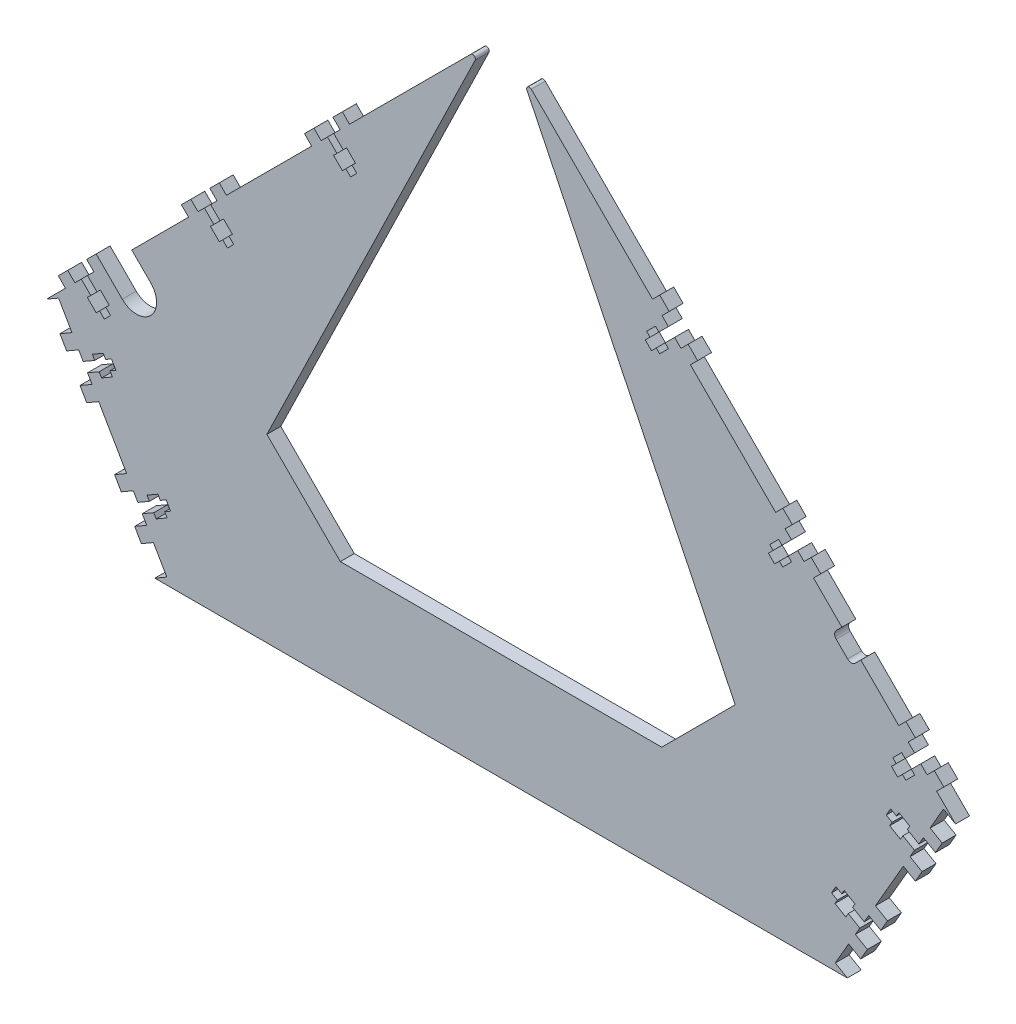
SolidWorks part; units mm, degrees
material "Acrylic (Blue)"
ref_plane "Front Plane" through (0, 0, 0) normal (0, 0, 1) x (1, 0, 0)
ref_plane "Top Plane" through (0, 0, 0) normal (0, 1, 0) x (1, 0, 0)
ref_plane "Right Plane" through (0, 0, 0) normal (1, 0, 0) x (0, 0, -1)
sketch "Sketch1" plane through (0, 0, 0) normal (0, 0, 1) x (1, 0, 0)
  line L0 (0, 0) -> (0, 304.4261) construction
  line L1 (0, 304.4261) -> (215.5261, 88.9)
  line L2 (215.5261, 88.9) -> (164.1997, 0)
  line L3 (164.1997, 0) -> (0, 0)
  line L4 (0, 304.4261) -> (-215.5261, 88.9)
  line L5 (-215.5261, 88.9) -> (-164.1997, 0)
  line L6 (-164.1997, 0) -> (0, 0)
  line L7 (-215.5261, 88.9) -> (215.5261, 88.9) construction
  line L8 (0, 304.4261) -> (3.5921, 308.0182) construction
  line L9 (3.5921, 308.0182) -> (219.1182, 92.4921) construction
  line L10 (219.1182, 92.4921) -> (215.5261, 88.9) construction
  line L11 (3.5921, 308.0182) -> (0, 311.6104) construction
  line L12 (0, 311.6104) -> (-219.1182, 92.4921) construction
  line L13 (-219.1182, 92.4921) -> (-215.5261, 88.9) construction
  line L14 (215.5261, 88.9) -> (219.9256, 86.36) construction
  line L15 (219.9256, 86.36) -> (168.5991, -2.54) construction
  line L16 (168.5991, -2.54) -> (164.1997, 0) construction
  line L17 (164.1997, 0) -> (164.1997, -12.7) construction
  line L18 (164.1997, -12.7) -> (-164.1997, -12.7) construction
  line L19 (-164.1997, -12.7) -> (-164.1997, 0) construction
  line L20 (-164.1997, 0) -> (-168.5991, -2.54) construction
  line L21 (-168.5991, -2.54) -> (-219.9256, 86.36) construction
  line L22 (-219.9256, 86.36) -> (-215.5261, 88.9) construction
  dimension "D1" = 304.8
  dimension "D2" = 120
  dimension "D3" = 88.9
  dimension "D4" = 5.08
  dimension "D5" = 12.7
extrude "Boss-Extrude1" add sketch "Sketch1" along normal blind 6.604
other "Move Face2" face at (107.7631, 196.6631, 3.302) parameters "D1"=0.0025
sketch "Sketch2" plane through (0, 0, 6.604) normal (0, 0, 1) x (1, 0, 0)
  line L0 (215.5275, 88.9023) -> (0.0018, 304.4279) construction
  line L1 (0, 0) -> (0, 311.15) construction
  line L2 (0, 50.8) -> (76.2, 50.8)
  line L3 (0.0018, 304.4279) -> (3.5939, 308.02) construction
  line L4 (76.2, 50.8) -> (111.0333, 85.6333)
  line L5 (8.9816, 295.4482) -> (-8.9803, 295.4459) construction
  line L6 (0.0018, 304.4279) -> (-215.5261, 88.9) construction
  line L7 (-8.9803, 295.4459) -> (-111.0333, 85.6333)
  line L8 (-164.1997, 0) -> (164.1997, 0) construction
  line L9 (111.0333, 85.6333) -> (8.9816, 295.4482)
  line L10 (3.5939, 308.02) -> (0.0018, 311.6121) construction
  line L11 (-8.9803, 295.4459) -> (0.0018, 304.4279)
  line L12 (-111.0333, 85.6333) -> (-76.2, 50.8)
  line L13 (-76.2, 50.8) -> (0, 50.8)
  line L14 (0.0018, 304.4279) -> (8.9816, 295.4482)
  line L15 (0.0018, 304.4279) -> (-215.5261, 88.9) construction
  dimension "D1" = 260.35
  dimension "D2" = 50.8
  dimension "D3" = 292.1
  dimension "D4" = 5.08
  dimension "D6" = 76.2
  dimension "D7" = 45
  dimension "D8" = 76.2
  dimension "D9" = 45
  dimension "D10" = 292.1
extrude "Cut-Extrude1" cut sketch "Sketch2" against normal through all
sketch "Sketch3" plane through (0, 0, 6.604) normal (0, 0, 1) x (1, 0, 0)
  line L0 (-209.8069, 92.202) -> (-215.5261, 88.9)
  line L1 (-215.5261, 88.9) -> (-164.1997, 0)
  line L2 (-164.1997, 0) -> (-158.4805, 3.302)
  line L3 (-158.4805, 3.302) -> (-209.8069, 92.202)
  line L4 (0, 304.4261) -> (0, 0) construction
  line L5 (158.4805, 3.302) -> (209.8069, 92.202)
  line L6 (164.1997, 0) -> (158.4805, 3.302)
  line L7 (215.5261, 88.9) -> (164.1997, 0)
  line L8 (209.8069, 92.202) -> (215.5261, 88.9)
  dimension "D1" = 6.604
extrude "Cut-Extrude2" cut sketch "Sketch3" against normal through all
sketch "Sketch4" plane through (0, 0, 6.604) normal (0, 0, 1) x (1, 0, 0)
  line L0 (-8.9803, 295.4459) -> (-215.5261, 88.9) construction
  line L1 (-93.2151, 218.0361) -> (-133.6262, 177.6249) construction
  line L2 (-8.9803, 295.4459) -> (-215.5261, 88.9) construction
  line L3 (-191.9979, 119.2533) -> (-151.5867, 159.6644) construction
  line L6 (215.5275, 88.9023) -> (8.9816, 295.4482) construction
  line L7 (93.2164, 218.0384) -> (133.6275, 177.6272) construction
  line L8 (-158.4805, 3.302) -> (-209.8069, 92.202) construction
  line L9 (-209.8069, 92.202) -> (-215.5261, 88.9) construction
  line L10 (151.588, 159.6667) -> (191.9992, 119.2555) construction
  line L11 (209.8069, 92.202) -> (158.4805, 3.302) construction
  line L12 (158.4805, 3.302) -> (164.1997, 0) construction
  line L13 (-164.1997, 0) -> (-158.4805, 3.302) construction
  line L14 (215.5261, 88.9) -> (209.8069, 92.202) construction
  line B0 (-82.2951, 222.1311) -> (-77.8049, 217.641) construction
  line B1 (-77.8049, 217.641) -> (-79.4214, 216.0245) construction
  line B2 (-79.4214, 216.0245) -> (-75.2186, 211.8217) construction
  line B3 (-75.2186, 211.8217) -> (-73.6022, 213.4382) construction
  line B4 (-73.6022, 213.4382) -> (-71.3392, 211.1752) construction
  line B5 (-71.3392, 211.1752) -> (-68.3936, 214.1207) construction
  line B6 (-68.3936, 214.1207) -> (-70.6567, 216.3837) construction
  line B7 (-70.6567, 216.3837) -> (-69.0402, 218.0002) construction
  line B8 (-69.0402, 218.0002) -> (-73.243, 222.2029) construction
  line B9 (-73.243, 222.2029) -> (-74.8594, 220.5865) construction
  line B10 (-74.8594, 220.5865) -> (-79.3495, 225.0766) construction
  line B11 (-76.3322, 228.094) -> (-79.7447, 231.5065) construction
  line B12 (-79.7447, 231.5065) -> (-75.2545, 235.9966) construction
  line B13 (-75.2545, 235.9966) -> (-71.842, 232.5841) construction
  line B14 (-82.2951, 222.1311) -> (-85.3124, 219.1137) construction
  line B15 (-85.3124, 219.1137) -> (-88.7249, 222.5262) construction
  line B16 (-88.7249, 222.5262) -> (-93.2151, 218.0361) construction
  line B17 (-93.2151, 218.0361) -> (-89.8026, 214.6236) construction
  line B18 (-79.3495, 225.0766) -> (-82.2951, 222.1311) construction
  line B19 (-199.0384, 105.3878) -> (-194.5483, 100.8976) construction
  line B20 (-194.5483, 100.8976) -> (-196.1647, 99.2812) construction
  line B21 (-196.1647, 99.2812) -> (-191.962, 95.0784) construction
  line B22 (-191.962, 95.0784) -> (-190.3455, 96.6949) construction
  line B23 (-190.3455, 96.6949) -> (-188.0825, 94.4318) construction
  line B24 (-188.0825, 94.4318) -> (-185.137, 97.3774) construction
  line B25 (-185.137, 97.3774) -> (-187.4, 99.6404) construction
  line B26 (-187.4, 99.6404) -> (-185.7835, 101.2568) construction
  line B27 (-185.7835, 101.2568) -> (-189.9863, 105.4596) construction
  line B28 (-189.9863, 105.4596) -> (-191.6027, 103.8431) construction
  line B29 (-191.6027, 103.8431) -> (-196.0929, 108.3333) construction
  line B30 (-196.0929, 108.3333) -> (-193.0755, 111.3506) construction
  line B31 (-193.0755, 111.3506) -> (-196.488, 114.7631) construction
  line B32 (-196.488, 114.7631) -> (-191.9979, 119.2533) construction
  line B33 (-191.9979, 119.2533) -> (-188.5854, 115.8408) construction
  line B34 (-199.0384, 105.3878) -> (-202.0558, 102.3704) construction
  line B35 (-202.0558, 102.3704) -> (-205.4683, 105.7829) construction
  line B36 (-205.4683, 105.7829) -> (-209.9584, 101.2928) construction
  line B37 (-209.9584, 101.2928) -> (-206.5459, 97.8803) construction
  line B38 (-196.0929, 108.3333) -> (-199.0384, 105.3878) construction
  line B39 (-170.1391, 23.4953) -> (-164.6398, 26.6703) construction
  line B40 (-164.6398, 26.6703) -> (-163.4968, 24.6906) construction
  line B41 (-163.4968, 24.6906) -> (-158.3495, 27.6624) construction
  line B42 (-158.3495, 27.6624) -> (-159.4925, 29.6421) construction
  line B43 (-159.4925, 29.6421) -> (-156.7209, 31.2423) construction
  line B44 (-156.7209, 31.2423) -> (-158.8037, 34.8498) construction
  line B45 (-158.8037, 34.8498) -> (-161.5753, 33.2496) construction
  line B46 (-161.5753, 33.2496) -> (-162.7183, 35.2293) construction
  line B47 (-162.7183, 35.2293) -> (-167.8656, 32.2575) construction
  line B48 (-167.8656, 32.2575) -> (-166.7226, 30.2778) construction
  line B49 (-166.7226, 30.2778) -> (-172.2219, 27.1028) construction
  line B50 (-172.2219, 27.1028) -> (-174.3555, 30.7983) construction
  line B51 (-174.3555, 30.7983) -> (-178.5349, 28.3853) construction
  line B52 (-178.5349, 28.3853) -> (-181.7099, 33.8846) construction
  line B53 (-181.7099, 33.8846) -> (-177.5305, 36.2976) construction
  line B54 (-168.0055, 19.7998) -> (-172.1849, 17.3868) construction
  line B55 (-172.1849, 17.3868) -> (-169.0099, 11.8875) construction
  line B56 (-169.0099, 11.8875) -> (-164.8305, 14.3005) construction
  line B57 (-172.2219, 27.1028) -> (-170.1391, 23.4953) construction
  line B58 (-196.0655, 68.4012) -> (-190.5663, 71.5762) construction
  line B59 (-190.5663, 71.5762) -> (-189.4233, 69.5965) construction
  line B60 (-189.4233, 69.5965) -> (-184.2759, 72.5683) construction
  line B61 (-184.2759, 72.5683) -> (-185.4189, 74.548) construction
  line B62 (-185.4189, 74.548) -> (-182.6473, 76.1482) construction
  line B63 (-182.6473, 76.1482) -> (-184.7301, 79.7557) construction
  line B64 (-184.7301, 79.7557) -> (-187.5017, 78.1555) construction
  line B65 (-187.5017, 78.1555) -> (-188.6447, 80.1352) construction
  line B66 (-188.6447, 80.1352) -> (-193.7921, 77.1634) construction
  line B67 (-193.7921, 77.1634) -> (-192.6491, 75.1837) construction
  line B68 (-192.6491, 75.1837) -> (-198.1483, 72.0087) construction
  line B69 (-198.1483, 72.0087) -> (-200.2819, 75.7042) construction
  line B70 (-200.2819, 75.7042) -> (-204.4614, 73.2912) construction
  line B71 (-204.4614, 73.2912) -> (-207.6364, 78.7905) construction
  line B72 (-207.6364, 78.7905) -> (-203.4569, 81.2035) construction
  line B73 (-196.0655, 68.4012) -> (-193.9319, 64.7057) construction
  line B74 (-193.9319, 64.7057) -> (-198.1114, 62.2927) construction
  line B75 (-198.1114, 62.2927) -> (-194.9364, 56.7934) construction
  line B76 (-194.9364, 56.7934) -> (-190.7569, 59.2064) construction
  line B77 (-198.1483, 72.0087) -> (-196.0655, 68.4012) construction
  line B78 (172.2219, 27.1028) -> (166.7226, 30.2778) construction
  line B79 (166.7226, 30.2778) -> (167.8656, 32.2575) construction
  line B80 (167.8656, 32.2575) -> (162.7183, 35.2293) construction
  line B81 (162.7183, 35.2293) -> (161.5753, 33.2496) construction
  line B82 (161.5753, 33.2496) -> (158.8037, 34.8498) construction
  line B83 (158.8037, 34.8498) -> (156.7209, 31.2423) construction
  line B84 (156.7209, 31.2423) -> (159.4925, 29.6421) construction
  line B85 (159.4925, 29.6421) -> (158.3495, 27.6624) construction
  line B86 (158.3495, 27.6624) -> (163.4968, 24.6906) construction
  line B87 (163.4968, 24.6906) -> (164.6398, 26.6703) construction
  line B88 (164.6398, 26.6703) -> (170.1391, 23.4953) construction
  line B89 (168.0055, 19.7998) -> (172.1849, 17.3868) construction
  line B90 (172.1849, 17.3868) -> (169.0099, 11.8875) construction
  line B91 (169.0099, 11.8875) -> (164.8305, 14.3005) construction
  line B92 (172.2219, 27.1028) -> (174.3555, 30.7983) construction
  line B93 (174.3555, 30.7983) -> (178.5349, 28.3853) construction
  line B94 (178.5349, 28.3853) -> (181.7099, 33.8846) construction
  line B95 (181.7099, 33.8846) -> (177.5305, 36.2976) construction
  line B96 (170.1391, 23.4953) -> (172.2219, 27.1028) construction
  line B97 (198.1483, 72.0087) -> (192.6491, 75.1837) construction
  line B98 (192.6491, 75.1837) -> (193.7921, 77.1634) construction
  line B99 (193.7921, 77.1634) -> (188.6447, 80.1352) construction
  line B100 (188.6447, 80.1352) -> (187.5017, 78.1555) construction
  line B101 (187.5017, 78.1555) -> (184.7301, 79.7557) construction
  line B102 (184.7301, 79.7557) -> (182.6473, 76.1482) construction
  line B103 (182.6473, 76.1482) -> (185.4189, 74.548) construction
  line B104 (185.4189, 74.548) -> (184.2759, 72.5683) construction
  line B105 (184.2759, 72.5683) -> (189.4233, 69.5965) construction
  line B106 (189.4233, 69.5965) -> (190.5663, 71.5762) construction
  line B107 (190.5663, 71.5762) -> (196.0655, 68.4012) construction
  line B108 (196.0655, 68.4012) -> (193.9319, 64.7057) construction
  line B109 (193.9319, 64.7057) -> (198.1114, 62.2927) construction
  line B110 (198.1114, 62.2927) -> (194.9364, 56.7934) construction
  line B111 (194.9364, 56.7934) -> (190.7569, 59.2064) construction
  line B112 (200.2819, 75.7042) -> (204.4614, 73.2912) construction
  line B113 (204.4614, 73.2912) -> (207.6364, 78.7905) construction
  line B114 (207.6364, 78.7905) -> (203.4569, 81.2035) construction
  line B115 (196.0655, 68.4012) -> (198.1483, 72.0087) construction
  line B116 (196.0942, 108.3356) -> (191.6041, 103.8454) construction
  line B117 (191.6041, 103.8454) -> (189.9876, 105.4619) construction
  line B118 (189.9876, 105.4619) -> (185.7849, 101.2591) construction
  line B119 (185.7849, 101.2591) -> (187.4013, 99.6427) construction
  line B120 (187.4013, 99.6427) -> (185.1383, 97.3796) construction
  line B121 (185.1383, 97.3796) -> (188.0838, 94.4341) construction
  line B122 (188.0838, 94.4341) -> (190.3468, 96.6971) construction
  line B123 (190.3468, 96.6971) -> (191.9633, 95.0807) construction
  line B124 (191.9633, 95.0807) -> (196.166, 99.2835) construction
  line B125 (196.166, 99.2835) -> (194.5496, 100.8999) construction
  line B126 (194.5496, 100.8999) -> (199.0397, 105.39) construction
  line B127 (199.0397, 105.39) -> (202.0571, 102.3727) construction
  line B128 (202.0571, 102.3727) -> (205.4696, 105.7852) construction
  line B129 (205.4696, 105.7852) -> (209.9597, 101.295) construction
  line B130 (209.9597, 101.295) -> (206.5472, 97.8825) construction
  line B131 (196.0942, 108.3356) -> (193.0768, 111.3529) construction
  line B132 (193.0768, 111.3529) -> (196.4893, 114.7654) construction
  line B133 (196.4893, 114.7654) -> (191.9992, 119.2555) construction
  line B134 (191.9992, 119.2555) -> (188.5867, 115.843) construction
  line B135 (199.0397, 105.39) -> (196.0942, 108.3356) construction
  line B136 (137.7225, 166.7072) -> (133.2324, 162.2171) construction
  line B137 (133.2324, 162.2171) -> (131.6159, 163.8335) construction
  line B138 (131.6159, 163.8335) -> (127.4132, 159.6308) construction
  line B139 (127.4132, 159.6308) -> (129.0296, 158.0143) construction
  line B140 (129.0296, 158.0143) -> (126.7666, 155.7513) construction
  line B141 (126.7666, 155.7513) -> (129.7121, 152.8058) construction
  line B142 (129.7121, 152.8058) -> (131.9752, 155.0688) construction
  line B143 (131.9752, 155.0688) -> (133.5916, 153.4524) construction
  line B144 (133.5916, 153.4524) -> (137.7944, 157.6551) construction
  line B145 (137.7944, 157.6551) -> (136.1779, 159.2716) construction
  line B146 (136.1779, 159.2716) -> (140.668, 163.7617) construction
  line B147 (140.668, 163.7617) -> (143.6854, 160.7443) construction
  line B148 (143.6854, 160.7443) -> (147.0979, 164.1568) construction
  line B149 (147.0979, 164.1568) -> (151.588, 159.6667) construction
  line B150 (151.588, 159.6667) -> (148.1755, 156.2542) construction
  line B151 (137.7225, 166.7072) -> (134.7052, 169.7246) construction
  line B152 (134.7052, 169.7246) -> (138.1177, 173.1371) construction
  line B153 (138.1177, 173.1371) -> (133.6275, 177.6272) construction
  line B154 (133.6275, 177.6272) -> (130.215, 174.2147) construction
  line B155 (140.668, 163.7617) -> (137.7225, 166.7072) construction
  line B156 (79.3509, 225.0789) -> (74.8607, 220.5888) construction
  line B157 (74.8607, 220.5888) -> (73.2443, 222.2052) construction
  line B158 (73.2443, 222.2052) -> (69.0415, 218.0024) construction
  line B159 (69.0415, 218.0024) -> (70.658, 216.386) construction
  line B160 (70.658, 216.386) -> (68.3949, 214.123) construction
  line B161 (68.3949, 214.123) -> (71.3405, 211.1774) construction
  line B162 (71.3405, 211.1774) -> (73.6035, 213.4405) construction
  line B163 (73.6035, 213.4405) -> (75.2199, 211.824) construction
  line B164 (75.2199, 211.824) -> (79.4227, 216.0268) construction
  line B165 (79.4227, 216.0268) -> (77.8063, 217.6432) construction
  line B166 (77.8063, 217.6432) -> (82.2964, 222.1334) construction
  line B167 (82.2964, 222.1334) -> (85.3137, 219.116) construction
  line B168 (85.3137, 219.116) -> (88.7262, 222.5285) construction
  line B169 (88.7262, 222.5285) -> (93.2164, 218.0384) construction
  line B170 (93.2164, 218.0384) -> (89.8039, 214.6259) construction
  line B171 (79.3509, 225.0789) -> (76.3335, 228.0962) construction
  line B172 (76.3335, 228.0962) -> (79.746, 231.5087) construction
  line B173 (79.746, 231.5087) -> (75.2559, 235.9989) construction
  line B174 (75.2559, 235.9989) -> (71.8434, 232.5864) construction
  line B175 (82.2964, 222.1334) -> (79.3509, 225.0789) construction
  line B176 (-140.6667, 163.7594) -> (-136.1766, 159.2693) construction
  line B177 (-136.1766, 159.2693) -> (-137.793, 157.6528) construction
  line B178 (-137.793, 157.6528) -> (-133.5903, 153.4501) construction
  line B179 (-133.5903, 153.4501) -> (-131.9738, 155.0665) construction
  line B180 (-131.9738, 155.0665) -> (-129.7108, 152.8035) construction
  line B181 (-129.7108, 152.8035) -> (-126.7653, 155.749) construction
  line B182 (-126.7653, 155.749) -> (-129.0283, 158.0121) construction
  line B183 (-129.0283, 158.0121) -> (-127.4119, 159.6285) construction
  line B184 (-127.4119, 159.6285) -> (-131.6146, 163.8313) construction
  line B185 (-131.6146, 163.8313) -> (-133.2311, 162.2148) construction
  line B186 (-133.2311, 162.2148) -> (-137.7212, 166.7049) construction
  line B187 (-137.7212, 166.7049) -> (-134.7038, 169.7223) construction
  line B188 (-134.7038, 169.7223) -> (-138.1163, 173.1348) construction
  line B189 (-138.1163, 173.1348) -> (-133.6262, 177.6249) construction
  line B190 (-133.6262, 177.6249) -> (-130.2137, 174.2124) construction
  line B191 (-140.6667, 163.7594) -> (-143.6841, 160.742) construction
  line B192 (-143.6841, 160.742) -> (-147.0966, 164.1545) construction
  line B193 (-147.0966, 164.1545) -> (-151.5867, 159.6644) construction
  line B194 (-151.5867, 159.6644) -> (-148.1742, 156.2519) construction
  line B195 (-137.7212, 166.7049) -> (-140.6667, 163.7594) construction
  dimension "D1" = 12.7
  dimension "D2" = 190.5
  dimension "D3" = 12.7
  dimension "D4" = 190.5
  dimension "D5" = 12.7
  dimension "D6" = 12.7
  dimension "D7" = 12.7
  dimension "D8" = 12.7
sketch_block_instance "NUT_HOLE-1"
sketch_block "NUT_HOLE" parameters "D1"=6.35, "D2"=4.1656, "D3"=25.4, "D4"=4.826, "D5"=8.7376, "D6"=5.9436, "D7"=6.35, "D8"=20.32
sketch_block_instance "NUT_HOLE-3"
sketch_block_instance "NUT_HOLE-9"
sketch_block_instance "NUT_HOLE-10"
sketch_block_instance "NUT_HOLE-11"
sketch_block_instance "NUT_HOLE-12"
sketch_block_instance "NUT_HOLE-13"
sketch_block_instance "NUT_HOLE-14"
sketch_block_instance "NUT_HOLE-15"
sketch_block_instance "NUT_HOLE-16"
sketch "Sketch6" plane through (0, 0, 6.604) normal (0, 0, 1) x (1, 0, 0)
  line L0 (-133.2311, 162.2148) -> (-137.7212, 166.7049) construction
  line L1 (-140.6667, 163.7594) -> (-136.1766, 159.2693) construction
  line L2 (-136.1766, 159.2693) -> (-137.793, 157.6528) construction
  line L3 (-137.793, 157.6528) -> (-133.5903, 153.4501) construction
  line L4 (-133.5903, 153.4501) -> (-131.9738, 155.0665) construction
  line L5 (-131.9738, 155.0665) -> (-129.7108, 152.8035) construction
  line L6 (-129.7108, 152.8035) -> (-126.7653, 155.749) construction
  line L7 (-126.7653, 155.749) -> (-129.0283, 158.0121) construction
  line L8 (-129.0283, 158.0121) -> (-127.4119, 159.6285) construction
  line L9 (-127.4119, 159.6285) -> (-131.6146, 163.8313) construction
  line L10 (-131.6146, 163.8313) -> (-133.2311, 162.2148) construction
  line L11 (-133.2311, 162.2148) -> (-137.7212, 166.7049)
  line L12 (-140.6667, 163.7594) -> (-136.1766, 159.2693)
  line L13 (-136.1766, 159.2693) -> (-137.793, 157.6528)
  line L14 (-137.793, 157.6528) -> (-133.5903, 153.4501)
  line L15 (-133.5903, 153.4501) -> (-131.9738, 155.0665)
  line L16 (-131.9738, 155.0665) -> (-129.7108, 152.8035)
  line L17 (-129.7108, 152.8035) -> (-126.7653, 155.749)
  line L18 (-126.7653, 155.749) -> (-129.0283, 158.0121)
  line L19 (-129.0283, 158.0121) -> (-127.4119, 159.6285)
  line L20 (-127.4119, 159.6285) -> (-131.6146, 163.8313)
  line L21 (-131.6146, 163.8313) -> (-133.2311, 162.2148)
  line L22 (-140.6667, 163.7594) -> (-137.7212, 166.7049)
  line L110 (-74.8594, 220.5865) -> (-79.3495, 225.0766) construction
  line L111 (-73.243, 222.2029) -> (-74.8594, 220.5865) construction
  line L112 (-69.0402, 218.0002) -> (-73.243, 222.2029) construction
  line L113 (-70.6567, 216.3837) -> (-69.0402, 218.0002) construction
  line L114 (-68.3936, 214.1207) -> (-70.6567, 216.3837) construction
  line L115 (-71.3392, 211.1752) -> (-68.3936, 214.1207) construction
  line L116 (-73.6022, 213.4382) -> (-71.3392, 211.1752) construction
  line L117 (-75.2186, 211.8217) -> (-73.6022, 213.4382) construction
  line L118 (-79.4214, 216.0245) -> (-75.2186, 211.8217) construction
  line L119 (-77.8049, 217.641) -> (-79.4214, 216.0245) construction
  line L120 (-82.2951, 222.1311) -> (-77.8049, 217.641) construction
  line L121 (-74.8594, 220.5865) -> (-79.3495, 225.0766)
  line L122 (-73.243, 222.2029) -> (-74.8594, 220.5865)
  line L123 (-69.0402, 218.0002) -> (-73.243, 222.2029)
  line L124 (-70.6567, 216.3837) -> (-69.0402, 218.0002)
  line L125 (-68.3936, 214.1207) -> (-70.6567, 216.3837)
  line L126 (-71.3392, 211.1752) -> (-68.3936, 214.1207)
  line L127 (-73.6022, 213.4382) -> (-71.3392, 211.1752)
  line L128 (-75.2186, 211.8217) -> (-73.6022, 213.4382)
  line L129 (-79.4214, 216.0245) -> (-75.2186, 211.8217)
  line L130 (-77.8049, 217.641) -> (-79.4214, 216.0245)
  line L131 (-82.2951, 222.1311) -> (-77.8049, 217.641)
  line L154 (-191.6027, 103.8431) -> (-196.0929, 108.3333) construction
  line L155 (-199.0384, 105.3878) -> (-194.5483, 100.8976) construction
  line L156 (-194.5483, 100.8976) -> (-196.1647, 99.2812) construction
  line L157 (-196.1647, 99.2812) -> (-191.962, 95.0784) construction
  line L158 (-189.9863, 105.4596) -> (-191.6027, 103.8431) construction
  line L159 (-185.7835, 101.2568) -> (-189.9863, 105.4596) construction
  line L160 (-187.4, 99.6404) -> (-185.7835, 101.2568) construction
  line L161 (-185.137, 97.3774) -> (-187.4, 99.6404) construction
  line L162 (-188.0825, 94.4318) -> (-185.137, 97.3774) construction
  line L163 (-190.3455, 96.6949) -> (-188.0825, 94.4318) construction
  line L164 (-191.962, 95.0784) -> (-190.3455, 96.6949) construction
  line L165 (-192.6491, 75.1837) -> (-198.1483, 72.0087) construction
  line L166 (-193.7921, 77.1634) -> (-192.6491, 75.1837) construction
  line L167 (-188.6447, 80.1352) -> (-193.7921, 77.1634) construction
  line L168 (-184.7301, 79.7557) -> (-187.5017, 78.1555) construction
  line L169 (-182.6473, 76.1482) -> (-184.7301, 79.7557) construction
  line L170 (-187.5017, 78.1555) -> (-188.6447, 80.1352) construction
  line L171 (-185.4189, 74.548) -> (-182.6473, 76.1482) construction
  line L172 (-184.2759, 72.5683) -> (-185.4189, 74.548) construction
  line L173 (-189.4233, 69.5965) -> (-184.2759, 72.5683) construction
  line L174 (-190.5663, 71.5762) -> (-189.4233, 69.5965) construction
  line L175 (-196.0655, 68.4012) -> (-190.5663, 71.5762) construction
  line L176 (-191.6027, 103.8431) -> (-196.0929, 108.3333)
  line L177 (-199.0384, 105.3878) -> (-194.5483, 100.8976)
  line L178 (-194.5483, 100.8976) -> (-196.1647, 99.2812)
  line L179 (-196.1647, 99.2812) -> (-191.962, 95.0784)
  line L180 (-189.9863, 105.4596) -> (-191.6027, 103.8431)
  line L181 (-185.7835, 101.2568) -> (-189.9863, 105.4596)
  line L182 (-187.4, 99.6404) -> (-185.7835, 101.2568)
  line L183 (-185.137, 97.3774) -> (-187.4, 99.6404)
  line L184 (-188.0825, 94.4318) -> (-185.137, 97.3774)
  line L185 (-190.3455, 96.6949) -> (-188.0825, 94.4318)
  line L186 (-191.962, 95.0784) -> (-190.3455, 96.6949)
  line L187 (-192.6491, 75.1837) -> (-198.1483, 72.0087)
  line L188 (-193.7921, 77.1634) -> (-192.6491, 75.1837)
  line L189 (-188.6447, 80.1352) -> (-193.7921, 77.1634)
  line L190 (-184.7301, 79.7557) -> (-187.5017, 78.1555)
  line L191 (-182.6473, 76.1482) -> (-184.7301, 79.7557)
  line L192 (-187.5017, 78.1555) -> (-188.6447, 80.1352)
  line L193 (-185.4189, 74.548) -> (-182.6473, 76.1482)
  line L194 (-184.2759, 72.5683) -> (-185.4189, 74.548)
  line L195 (-189.4233, 69.5965) -> (-184.2759, 72.5683)
  line L196 (-190.5663, 71.5762) -> (-189.4233, 69.5965)
  line L197 (-196.0655, 68.4012) -> (-190.5663, 71.5762)
  line L198 (-166.7226, 30.2778) -> (-172.2219, 27.1028) construction
  line L199 (-167.8656, 32.2575) -> (-166.7226, 30.2778) construction
  line L200 (-162.7183, 35.2293) -> (-167.8656, 32.2575) construction
  line L201 (-161.5753, 33.2496) -> (-162.7183, 35.2293) construction
  line L202 (-158.8037, 34.8498) -> (-161.5753, 33.2496) construction
  line L203 (-156.7209, 31.2423) -> (-158.8037, 34.8498) construction
  line L204 (-159.4925, 29.6421) -> (-156.7209, 31.2423) construction
  line L205 (-158.3495, 27.6624) -> (-159.4925, 29.6421) construction
  line L206 (-163.4968, 24.6906) -> (-158.3495, 27.6624) construction
  line L207 (-164.6398, 26.6703) -> (-163.4968, 24.6906) construction
  line L208 (-170.1391, 23.4953) -> (-164.6398, 26.6703) construction
  line L209 (-166.7226, 30.2778) -> (-172.2219, 27.1028)
  line L210 (-167.8656, 32.2575) -> (-166.7226, 30.2778)
  line L211 (-162.7183, 35.2293) -> (-167.8656, 32.2575)
  line L212 (-161.5753, 33.2496) -> (-162.7183, 35.2293)
  line L213 (-158.8037, 34.8498) -> (-161.5753, 33.2496)
  line L214 (-156.7209, 31.2423) -> (-158.8037, 34.8498)
  line L215 (-159.4925, 29.6421) -> (-156.7209, 31.2423)
  line L216 (-158.3495, 27.6624) -> (-159.4925, 29.6421)
  line L217 (-163.4968, 24.6906) -> (-158.3495, 27.6624)
  line L218 (-164.6398, 26.6703) -> (-163.4968, 24.6906)
  line L219 (-170.1391, 23.4953) -> (-164.6398, 26.6703)
  line L220 (158.3495, 27.6624) -> (163.4968, 24.6906) construction
  line L221 (159.4925, 29.6421) -> (158.3495, 27.6624) construction
  line L222 (156.7209, 31.2423) -> (159.4925, 29.6421) construction
  line L223 (158.8037, 34.8498) -> (156.7209, 31.2423) construction
  line L224 (161.5753, 33.2496) -> (158.8037, 34.8498) construction
  line L225 (167.8656, 32.2575) -> (162.7183, 35.2293) construction
  line L226 (162.7183, 35.2293) -> (161.5753, 33.2496) construction
  line L227 (172.2219, 27.1028) -> (166.7226, 30.2778) construction
  line L228 (164.6398, 26.6703) -> (170.1391, 23.4953) construction
  line L229 (163.4968, 24.6906) -> (164.6398, 26.6703) construction
  line L230 (166.7226, 30.2778) -> (167.8656, 32.2575) construction
  line L231 (198.1483, 72.0087) -> (192.6491, 75.1837) construction
  line L232 (192.6491, 75.1837) -> (193.7921, 77.1634) construction
  line L233 (193.7921, 77.1634) -> (188.6447, 80.1352) construction
  line L234 (188.6447, 80.1352) -> (187.5017, 78.1555) construction
  line L235 (187.5017, 78.1555) -> (184.7301, 79.7557) construction
  line L236 (184.7301, 79.7557) -> (182.6473, 76.1482) construction
  line L237 (182.6473, 76.1482) -> (185.4189, 74.548) construction
  line L238 (185.4189, 74.548) -> (184.2759, 72.5683) construction
  line L239 (184.2759, 72.5683) -> (189.4233, 69.5965) construction
  line L240 (189.4233, 69.5965) -> (190.5663, 71.5762) construction
  line L241 (190.5663, 71.5762) -> (196.0655, 68.4012) construction
  line L242 (158.3495, 27.6624) -> (163.4968, 24.6906)
  line L243 (159.4925, 29.6421) -> (158.3495, 27.6624)
  line L244 (156.7209, 31.2423) -> (159.4925, 29.6421)
  line L245 (158.8037, 34.8498) -> (156.7209, 31.2423)
  line L246 (161.5753, 33.2496) -> (158.8037, 34.8498)
  line L247 (167.8656, 32.2575) -> (162.7183, 35.2293)
  line L248 (162.7183, 35.2293) -> (161.5753, 33.2496)
  line L249 (172.2219, 27.1028) -> (166.7226, 30.2778)
  line L250 (164.6398, 26.6703) -> (170.1391, 23.4953)
  line L251 (163.4968, 24.6906) -> (164.6398, 26.6703)
  line L252 (166.7226, 30.2778) -> (167.8656, 32.2575)
  line L253 (198.1483, 72.0087) -> (192.6491, 75.1837)
  line L254 (192.6491, 75.1837) -> (193.7921, 77.1634)
  line L255 (193.7921, 77.1634) -> (188.6447, 80.1352)
  line L256 (188.6447, 80.1352) -> (187.5017, 78.1555)
  line L257 (187.5017, 78.1555) -> (184.7301, 79.7557)
  line L258 (184.7301, 79.7557) -> (182.6473, 76.1482)
  line L259 (182.6473, 76.1482) -> (185.4189, 74.548)
  line L260 (185.4189, 74.548) -> (184.2759, 72.5683)
  line L261 (184.2759, 72.5683) -> (189.4233, 69.5965)
  line L262 (189.4233, 69.5965) -> (190.5663, 71.5762)
  line L263 (190.5663, 71.5762) -> (196.0655, 68.4012)
  line L264 (187.4013, 99.6427) -> (185.1383, 97.3796) construction
  line L265 (185.1383, 97.3796) -> (188.0838, 94.4341) construction
  line L266 (188.0838, 94.4341) -> (190.3468, 96.6971) construction
  line L267 (190.3468, 96.6971) -> (191.9633, 95.0807) construction
  line L268 (191.9633, 95.0807) -> (196.166, 99.2835) construction
  line L269 (196.166, 99.2835) -> (194.5496, 100.8999) construction
  line L270 (194.5496, 100.8999) -> (199.0397, 105.39) construction
  line L271 (196.0942, 108.3356) -> (191.6041, 103.8454) construction
  line L272 (191.6041, 103.8454) -> (189.9876, 105.4619) construction
  line L273 (189.9876, 105.4619) -> (185.7849, 101.2591) construction
  line L274 (185.7849, 101.2591) -> (187.4013, 99.6427) construction
  line L275 (187.4013, 99.6427) -> (185.1383, 97.3796)
  line L276 (185.1383, 97.3796) -> (188.0838, 94.4341)
  line L277 (188.0838, 94.4341) -> (190.3468, 96.6971)
  line L278 (190.3468, 96.6971) -> (191.9633, 95.0807)
  line L279 (191.9633, 95.0807) -> (196.166, 99.2835)
  line L280 (196.166, 99.2835) -> (194.5496, 100.8999)
  line L281 (194.5496, 100.8999) -> (199.0397, 105.39)
  line L282 (196.0942, 108.3356) -> (191.6041, 103.8454)
  line L283 (191.6041, 103.8454) -> (189.9876, 105.4619)
  line L284 (189.9876, 105.4619) -> (185.7849, 101.2591)
  line L285 (185.7849, 101.2591) -> (187.4013, 99.6427)
  line L286 (137.7225, 166.7072) -> (133.2324, 162.2171) construction
  line L287 (133.2324, 162.2171) -> (131.6159, 163.8335) construction
  line L288 (131.6159, 163.8335) -> (127.4132, 159.6308) construction
  line L289 (127.4132, 159.6308) -> (129.0296, 158.0143) construction
  line L290 (129.0296, 158.0143) -> (126.7666, 155.7513) construction
  line L291 (126.7666, 155.7513) -> (129.7121, 152.8058) construction
  line L292 (129.7121, 152.8058) -> (131.9752, 155.0688) construction
  line L293 (131.9752, 155.0688) -> (133.5916, 153.4524) construction
  line L294 (133.5916, 153.4524) -> (137.7944, 157.6551) construction
  line L295 (137.7944, 157.6551) -> (136.1779, 159.2716) construction
  line L296 (136.1779, 159.2716) -> (140.668, 163.7617) construction
  line L297 (137.7225, 166.7072) -> (133.2324, 162.2171)
  line L298 (133.2324, 162.2171) -> (131.6159, 163.8335)
  line L299 (131.6159, 163.8335) -> (127.4132, 159.6308)
  line L300 (127.4132, 159.6308) -> (129.0296, 158.0143)
  line L301 (129.0296, 158.0143) -> (126.7666, 155.7513)
  line L302 (126.7666, 155.7513) -> (129.7121, 152.8058)
  line L303 (129.7121, 152.8058) -> (131.9752, 155.0688)
  line L304 (131.9752, 155.0688) -> (133.5916, 153.4524)
  line L305 (133.5916, 153.4524) -> (137.7944, 157.6551)
  line L306 (137.7944, 157.6551) -> (136.1779, 159.2716)
  line L307 (136.1779, 159.2716) -> (140.668, 163.7617)
  line L308 (68.3949, 214.123) -> (71.3405, 211.1774) construction
  line L309 (71.3405, 211.1774) -> (73.6035, 213.4405) construction
  line L310 (73.6035, 213.4405) -> (75.2199, 211.824) construction
  line L311 (75.2199, 211.824) -> (79.4227, 216.0268) construction
  line L312 (77.8063, 217.6432) -> (82.2964, 222.1334) construction
  line L313 (79.4227, 216.0268) -> (77.8063, 217.6432) construction
  line L314 (79.3509, 225.0789) -> (74.8607, 220.5888) construction
  line L315 (74.8607, 220.5888) -> (73.2443, 222.2052) construction
  line L316 (73.2443, 222.2052) -> (69.0415, 218.0024) construction
  line L317 (69.0415, 218.0024) -> (70.658, 216.386) construction
  line L318 (70.658, 216.386) -> (68.3949, 214.123) construction
  line L319 (68.3949, 214.123) -> (71.3405, 211.1774)
  line L320 (71.3405, 211.1774) -> (73.6035, 213.4405)
  line L321 (73.6035, 213.4405) -> (75.2199, 211.824)
  line L322 (75.2199, 211.824) -> (79.4227, 216.0268)
  line L323 (77.8063, 217.6432) -> (82.2964, 222.1334)
  line L324 (79.4227, 216.0268) -> (77.8063, 217.6432)
  line L325 (79.3509, 225.0789) -> (74.8607, 220.5888)
  line L326 (74.8607, 220.5888) -> (73.2443, 222.2052)
  line L327 (73.2443, 222.2052) -> (69.0415, 218.0024)
  line L328 (69.0415, 218.0024) -> (70.658, 216.386)
  line L329 (70.658, 216.386) -> (68.3949, 214.123)
  line L330 (-79.3495, 225.0766) -> (-82.2951, 222.1311)
  line L332 (-196.0929, 108.3333) -> (-199.0384, 105.3878)
  line L333 (-198.1483, 72.0087) -> (-196.0655, 68.4012)
  line L334 (-172.2219, 27.1028) -> (-170.1391, 23.4953)
  line L335 (170.1391, 23.4953) -> (172.2219, 27.1028)
  line L336 (196.0655, 68.4012) -> (198.1483, 72.0087)
  line L337 (196.0942, 108.3356) -> (199.0397, 105.39)
  line L338 (137.7225, 166.7072) -> (140.668, 163.7617)
  line L339 (79.3509, 225.0789) -> (82.2964, 222.1334)
  point P61 (162.7183, 35.2293)
extrude "Cut-Extrude3" cut sketch "Sketch6" against normal through all
sketch "Sketch7" plane through (0, 0, 6.604) normal (0, 0, 1) x (1, 0, 0)
  line L0 (-133.6262, 177.6249) -> (-130.2137, 174.2124) construction
  line L1 (-138.1163, 173.1348) -> (-133.6262, 177.6249) construction
  line L2 (-134.7038, 169.7223) -> (-138.1163, 173.1348) construction
  line L3 (-143.6841, 160.742) -> (-147.0966, 164.1545) construction
  line L4 (-147.0966, 164.1545) -> (-151.5867, 159.6644) construction
  line L5 (-151.5867, 159.6644) -> (-148.1742, 156.2519) construction
  line L6 (-133.6262, 177.6249) -> (-130.2137, 174.2124)
  line L7 (-138.1163, 173.1348) -> (-133.6262, 177.6249)
  line L8 (-134.7038, 169.7223) -> (-138.1163, 173.1348)
  line L9 (-143.6841, 160.742) -> (-147.0966, 164.1545)
  line L10 (-147.0966, 164.1545) -> (-151.5867, 159.6644)
  line L11 (-151.5867, 159.6644) -> (-148.1742, 156.2519)
  line L12 (-130.2137, 174.2124) -> (-134.7038, 169.7223)
  line L13 (-143.6841, 160.742) -> (-148.1742, 156.2519)
  line L60 (-75.2545, 235.9966) -> (-71.842, 232.5841) construction
  line L61 (-79.7447, 231.5065) -> (-75.2545, 235.9966) construction
  line L62 (-76.3322, 228.094) -> (-79.7447, 231.5065) construction
  line L63 (-85.3124, 219.1137) -> (-88.7249, 222.5262) construction
  line L64 (-88.7249, 222.5262) -> (-93.2151, 218.0361) construction
  line L65 (-93.2151, 218.0361) -> (-89.8026, 214.6236) construction
  line L72 (-191.9979, 119.2533) -> (-188.5854, 115.8408) construction
  line L73 (-196.488, 114.7631) -> (-191.9979, 119.2533) construction
  line L74 (-193.0755, 111.3506) -> (-196.488, 114.7631) construction
  line L75 (-202.0558, 102.3704) -> (-205.4683, 105.7829) construction
  line L76 (-205.4683, 105.7829) -> (-209.9584, 101.2928) construction
  line L77 (-209.9584, 101.2928) -> (-206.5459, 97.8803) construction
  line L78 (-207.6364, 78.7905) -> (-203.4569, 81.2035) construction
  line L79 (-204.4614, 73.2912) -> (-207.6364, 78.7905) construction
  line L80 (-200.2819, 75.7042) -> (-204.4614, 73.2912) construction
  line L81 (-75.2545, 235.9966) -> (-71.842, 232.5841)
  line L82 (-79.7447, 231.5065) -> (-75.2545, 235.9966)
  line L83 (-76.3322, 228.094) -> (-79.7447, 231.5065)
  line L84 (-85.3124, 219.1137) -> (-88.7249, 222.5262)
  line L85 (-88.7249, 222.5262) -> (-93.2151, 218.0361)
  line L86 (-93.2151, 218.0361) -> (-89.8026, 214.6236)
  line L93 (-191.9979, 119.2533) -> (-188.5854, 115.8408)
  line L94 (-196.488, 114.7631) -> (-191.9979, 119.2533)
  line L95 (-193.0755, 111.3506) -> (-196.488, 114.7631)
  line L96 (-202.0558, 102.3704) -> (-205.4683, 105.7829)
  line L97 (-205.4683, 105.7829) -> (-209.9584, 101.2928)
  line L98 (-209.9584, 101.2928) -> (-206.5459, 97.8803)
  line L99 (-207.6364, 78.7905) -> (-203.4569, 81.2035)
  line L100 (-204.4614, 73.2912) -> (-207.6364, 78.7905)
  line L101 (-200.2819, 75.7042) -> (-204.4614, 73.2912)
  line L102 (-193.9319, 64.7057) -> (-198.1114, 62.2927) construction
  line L103 (-198.1114, 62.2927) -> (-194.9364, 56.7934) construction
  line L104 (-194.9364, 56.7934) -> (-190.7569, 59.2064) construction
  line L105 (-178.5349, 28.3853) -> (-181.7099, 33.8846) construction
  line L106 (-181.7099, 33.8846) -> (-177.5305, 36.2976) construction
  line L107 (-174.3555, 30.7983) -> (-178.5349, 28.3853) construction
  line L108 (-172.1849, 17.3868) -> (-169.0099, 11.8875) construction
  line L109 (-168.0055, 19.7998) -> (-172.1849, 17.3868) construction
  line L110 (-169.0099, 11.8875) -> (-164.8305, 14.3005) construction
  line L111 (169.0099, 11.8875) -> (164.8305, 14.3005) construction
  line L112 (172.1849, 17.3868) -> (169.0099, 11.8875) construction
  line L113 (168.0055, 19.7998) -> (172.1849, 17.3868) construction
  line L114 (181.7099, 33.8846) -> (177.5305, 36.2976) construction
  line L115 (178.5349, 28.3853) -> (181.7099, 33.8846) construction
  line L116 (174.3555, 30.7983) -> (178.5349, 28.3853) construction
  line L117 (193.9319, 64.7057) -> (198.1114, 62.2927) construction
  line L118 (198.1114, 62.2927) -> (194.9364, 56.7934) construction
  line L119 (194.9364, 56.7934) -> (190.7569, 59.2064) construction
  line L120 (207.6364, 78.7905) -> (203.4569, 81.2035) construction
  line L121 (200.2819, 75.7042) -> (204.4614, 73.2912) construction
  line L122 (204.4614, 73.2912) -> (207.6364, 78.7905) construction
  line L123 (-193.9319, 64.7057) -> (-198.1114, 62.2927)
  line L124 (-198.1114, 62.2927) -> (-194.9364, 56.7934)
  line L125 (-194.9364, 56.7934) -> (-190.7569, 59.2064)
  line L126 (-178.5349, 28.3853) -> (-181.7099, 33.8846)
  line L127 (-181.7099, 33.8846) -> (-177.5305, 36.2976)
  line L128 (-174.3555, 30.7983) -> (-178.5349, 28.3853)
  line L129 (-172.1849, 17.3868) -> (-169.0099, 11.8875)
  line L130 (-168.0055, 19.7998) -> (-172.1849, 17.3868)
  line L131 (-169.0099, 11.8875) -> (-164.8305, 14.3005)
  line L132 (169.0099, 11.8875) -> (164.8305, 14.3005)
  line L133 (172.1849, 17.3868) -> (169.0099, 11.8875)
  line L134 (168.0055, 19.7998) -> (172.1849, 17.3868)
  line L135 (181.7099, 33.8846) -> (177.5305, 36.2976)
  line L136 (178.5349, 28.3853) -> (181.7099, 33.8846)
  line L137 (174.3555, 30.7983) -> (178.5349, 28.3853)
  line L138 (193.9319, 64.7057) -> (198.1114, 62.2927)
  line L139 (198.1114, 62.2927) -> (194.9364, 56.7934)
  line L140 (194.9364, 56.7934) -> (190.7569, 59.2064)
  line L141 (207.6364, 78.7905) -> (203.4569, 81.2035)
  line L142 (200.2819, 75.7042) -> (204.4614, 73.2912)
  line L143 (204.4614, 73.2912) -> (207.6364, 78.7905)
  line L144 (209.9597, 101.295) -> (206.5472, 97.8825) construction
  line L145 (205.4696, 105.7852) -> (209.9597, 101.295) construction
  line L146 (202.0571, 102.3727) -> (205.4696, 105.7852) construction
  line L147 (193.0768, 111.3529) -> (196.4893, 114.7654) construction
  line L148 (196.4893, 114.7654) -> (191.9992, 119.2555) construction
  line L149 (191.9992, 119.2555) -> (188.5867, 115.843) construction
  line L150 (143.6854, 160.7443) -> (147.0979, 164.1568) construction
  line L151 (147.0979, 164.1568) -> (151.588, 159.6667) construction
  line L152 (151.588, 159.6667) -> (148.1755, 156.2542) construction
  line L153 (134.7052, 169.7246) -> (138.1177, 173.1371) construction
  line L154 (138.1177, 173.1371) -> (133.6275, 177.6272) construction
  line L155 (133.6275, 177.6272) -> (130.215, 174.2147) construction
  line L156 (209.9597, 101.295) -> (206.5472, 97.8825)
  line L157 (205.4696, 105.7852) -> (209.9597, 101.295)
  line L158 (202.0571, 102.3727) -> (205.4696, 105.7852)
  line L159 (193.0768, 111.3529) -> (196.4893, 114.7654)
  line L160 (196.4893, 114.7654) -> (191.9992, 119.2555)
  line L161 (191.9992, 119.2555) -> (188.5867, 115.843)
  line L162 (143.6854, 160.7443) -> (147.0979, 164.1568)
  line L163 (147.0979, 164.1568) -> (151.588, 159.6667)
  line L164 (151.588, 159.6667) -> (148.1755, 156.2542)
  line L165 (134.7052, 169.7246) -> (138.1177, 173.1371)
  line L166 (138.1177, 173.1371) -> (133.6275, 177.6272)
  line L167 (133.6275, 177.6272) -> (130.215, 174.2147)
  line L168 (75.2559, 235.9989) -> (71.8434, 232.5864) construction
  line L169 (79.746, 231.5087) -> (75.2559, 235.9989) construction
  line L170 (76.3335, 228.0962) -> (79.746, 231.5087) construction
  line L171 (85.3137, 219.116) -> (88.7262, 222.5285) construction
  line L172 (88.7262, 222.5285) -> (93.2164, 218.0384) construction
  line L173 (93.2164, 218.0384) -> (89.8039, 214.6259) construction
  line L174 (75.2559, 235.9989) -> (71.8434, 232.5864)
  line L175 (79.746, 231.5087) -> (75.2559, 235.9989)
  line L176 (76.3335, 228.0962) -> (79.746, 231.5087)
  line L177 (85.3137, 219.116) -> (88.7262, 222.5285)
  line L178 (88.7262, 222.5285) -> (93.2164, 218.0384)
  line L179 (93.2164, 218.0384) -> (89.8039, 214.6259)
  line L180 (71.8434, 232.5864) -> (76.3335, 228.0962)
  line L181 (85.3137, 219.116) -> (89.8039, 214.6259)
  line L182 (130.215, 174.2147) -> (134.7052, 169.7246)
  line L183 (143.6854, 160.7443) -> (148.1755, 156.2542)
  line L184 (188.5867, 115.843) -> (193.0768, 111.3529)
  line L185 (202.0571, 102.3727) -> (206.5472, 97.8825)
  line L186 (203.4569, 81.2035) -> (200.2819, 75.7042)
  line L187 (193.9319, 64.7057) -> (190.7569, 59.2064)
  line L188 (177.5305, 36.2976) -> (174.3555, 30.7983)
  line L189 (-168.0055, 19.7998) -> (-164.8305, 14.3005)
  line L190 (168.0055, 19.7998) -> (164.8305, 14.3005)
  line L191 (-177.5305, 36.2976) -> (-174.3555, 30.7983)
  line L192 (-193.9319, 64.7057) -> (-190.7569, 59.2064)
  line L193 (-203.4569, 81.2035) -> (-200.2819, 75.7042)
  line L194 (-206.5459, 97.8803) -> (-202.0558, 102.3704)
  line L195 (-193.0755, 111.3506) -> (-188.5854, 115.8408)
  line L198 (-71.842, 232.5841) -> (-76.3322, 228.094)
  line L199 (-85.3124, 219.1137) -> (-89.8026, 214.6236)
extrude "Boss-Extrude2" add sketch "Sketch7" against normal up to surface (6.604 mm away) up to face at (1.5969, 113.138, 0)
sketch "Sketch10" plane through (0, 0, 6.604) normal (0, 0, 1) x (1, 0, 0)
  line L0 (161.6459, 142.7838) -> (158.9518, 140.0897)
  line L1 (188.5867, 115.843) -> (148.1755, 156.2542) construction
  line L2 (158.9518, 136.4976) -> (164.34, 131.1095)
  line L3 (167.9321, 131.1095) -> (170.6262, 133.8036)
  line L4 (170.6262, 133.8036) -> (161.6459, 142.7838)
  line L5 (191.9992, 119.2555) -> (188.5867, 115.843) construction
  arc A0 (158.9518, 136.4976) -> (158.9518, 140.0897) centre (160.7479, 138.2937) cw
  arc A1 (167.9321, 131.1095) -> (164.34, 131.1095) centre (166.1361, 132.9055) cw
  point P10 (157.1558, 138.2937)
  dimension "D4" = 2.54
  dimension "D1" = 6.35
  dimension "D2" = 12.7
  dimension "D3" = 25.4
extrude "Cut-Extrude6" cut sketch "Sketch10" against normal through all
fillet "Fillet1" radius 1.27 2 edges at (8.9816, 295.4482, 3.302) (-8.9803, 295.4459, 3.302)
fillet "Fillet2" [suppressed] radius 6.35
other "Move Face3" face at (206.0489, 76.0408, 3.302) face at (196.5239, 59.5431, 3.302) face at (180.1224, 31.1349, 3.302) face at (170.5974, 14.6372, 3.302) face at (-170.5974, 14.6372, 3.302) face at (-180.1224, 31.1349, 3.302) face at (-196.5239, 59.5431, 3.302) face at (-206.0489, 76.0408, 3.302) parameters "D1"=1.778
sketch "Sketch8" plane through (0, 0, 6.604) normal (0, 0, 1) x (1, 0, 0)
  line L0 (-188.5854, 115.8408) -> (-179.6051, 106.8605)
  line L1 (-89.8026, 214.6236) -> (-130.2137, 174.2124) construction
  line L2 (-175.115, 129.3112) -> (-166.1347, 120.3309)
  line L3 (-71.842, 232.5841) -> (-75.2545, 235.9966) construction
  line L4 (-175.115, 129.3112) -> (-188.5854, 115.8408)
  arc A0 (-179.6051, 106.8605) -> (-166.1347, 120.3309) centre (-172.8699, 113.5957) ccw
  dimension "D1" = 12.7
  dimension "D2" = 19.05
  dimension "D3" = 146.05
extrude "Cut-Extrude5" cut sketch "Sketch8" against normal through all contours L0 A0 L2 L4
other "Move Face4" [suppressed] parameters "D1"=0.0508
